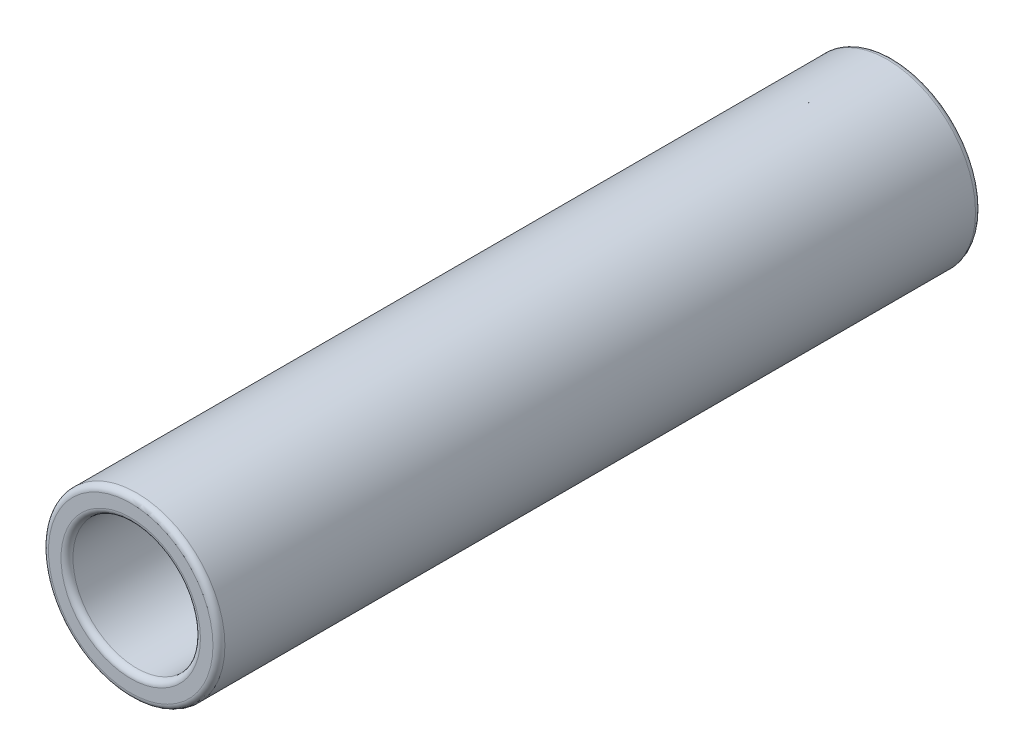
SolidWorks part; units mm, degrees
ref_plane "Front Plane" through (0, 0, 0) normal (0, 0, 1) x (1, 0, 0)
ref_plane "Top Plane" through (0, 0, 0) normal (0, 1, 0) x (1, 0, 0)
ref_plane "Right Plane" through (0, 0, 0) normal (1, 0, 0) x (0, 0, -1)
sketch "Sketch1" plane through (0, 0, 0) normal (0, 0, 1) x (1, 0, 0)
  circle A0 centre (0, 0) radius 5.9
extrude "Extrude1" add sketch "Sketch1" along normal blind 51
sketch "Sketch2" plane through (0, 0, 51) normal (0, 0, 1) x (1, 0, 0)
  circle A0 centre (0, 0) radius 4.2633
extrude "Extrude2" cut sketch "Sketch2" against normal through all
fillet "Fillet1" radius 0.4 4 edges at (5.9, 0, 0) (5.9, 0, 51) (4.2633, 0, 51) (4.2633, 0, 0)
sketch "Sketch3" plane through (0, 0, 0) normal (0, 1, 0) x (1, 0, 0)
  line L1 (-4.4039, -0.5902) -> (-4.0797, -0.5902)
  line L2 (-4.4039, -0.5902) -> (-4.4039, -0.8279)
  line L3 (-4.4039, -0.8279) -> (-4.0797, -0.8279)
  line L4 (-4.0797, -0.5902) -> (-4.0797, -0.8279)
sweep "Cut-Sweep2" cut profiles "Sketch3" path edge at (4.2633, 0, 0.4)
